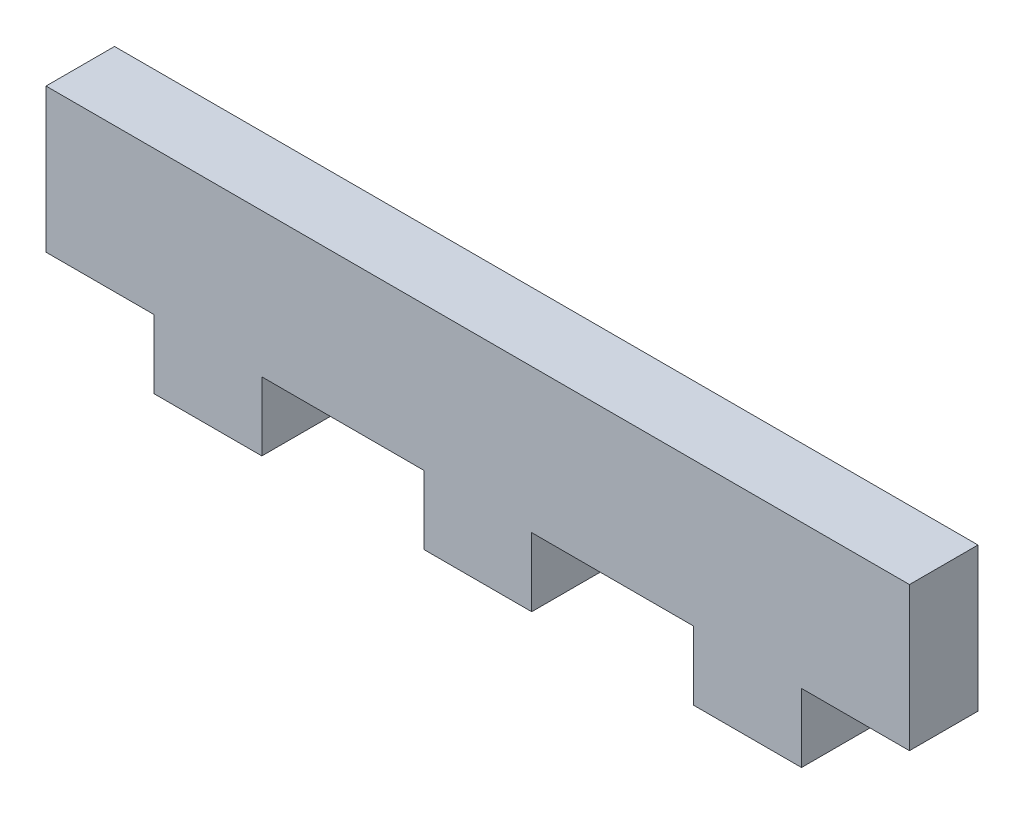
SolidWorks part; units mm, degrees
ref_plane "Front Plane" through (0, 0, 0) normal (0, 0, 1) x (1, 0, 0)
ref_plane "Top Plane" through (0, 0, 0) normal (0, 1, 0) x (1, 0, 0)
ref_plane "Right Plane" through (0, 0, 0) normal (1, 0, 0) x (0, 0, -1)
sketch "Sketch1" plane through (0, 0, 0) normal (0, 0, 1) x (1, 0, 0)
  line L0 (0, 0) -> (0, -6.5083) construction
  line L1 (-20, -3.3333) -> (-15, -3.3333)
  line L2 (-20, -3.3333) -> (-20, 3.3333)
  line L3 (-20, 3.3333) -> (20, 3.3333)
  line L4 (20, -3.3333) -> (20, 3.3333)
  line L5 (-20, -3.3333) -> (20, 3.3333) construction
  line L6 (-20, 3.3333) -> (20, -3.3333) construction
  line L8 (-15, -3.3333) -> (-15, -6.5083)
  line L9 (-15, -6.5083) -> (-10, -6.5083)
  line L10 (-10, -3.3333) -> (-10, -6.5083)
  line L12 (-2.5, -3.3333) -> (-2.5, -6.5083)
  line L13 (-2.5, -6.5083) -> (2.5, -6.5083)
  line L14 (2.5, -3.3333) -> (2.5, -6.5083)
  line L16 (10, -3.3333) -> (10, -6.5083)
  line L17 (10, -6.5083) -> (15, -6.5083)
  line L18 (15, -3.3333) -> (15, -6.5083)
  line L19 (-10, -3.3333) -> (-2.5, -3.3333)
  line L20 (2.5, -3.3333) -> (10, -3.3333)
  line L21 (15, -3.3333) -> (20, -3.3333)
  point P0 (0, 0)
  point P20 (0, 0)
  point P21 (0, -6.5083)
  dimension "D1" = 5
  dimension "D2" = 5
  dimension "D3" = 5
  dimension "D4" = 7.5
  dimension "D5" = 7.5
  dimension "D6" = 40
  dimension "D7" = 6.6667
  dimension "D8" = 3.175
  dimension "D9" = 3.175
  dimension "D10" = 3.175
extrude "Boss-Extrude1" add sketch "Sketch1" along normal blind 3.175
